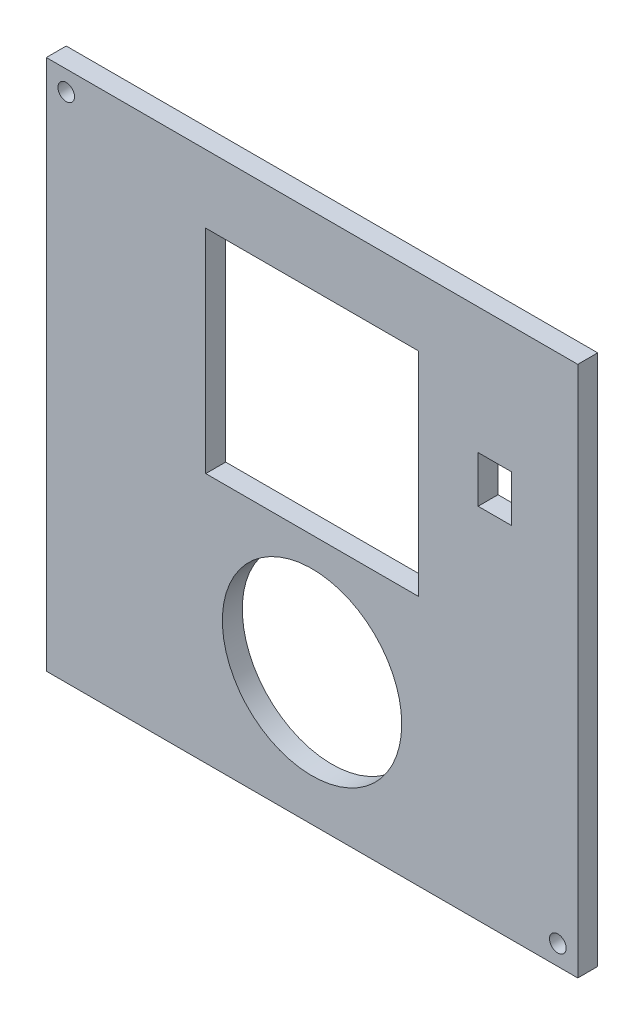
SolidWorks part; units mm, degrees
ref_plane "Front Plane" through (0, 0, 0) normal (0, 0, 1) x (1, 0, 0)
ref_plane "Top Plane" through (0, 0, 0) normal (0, 1, 0) x (1, 0, 0)
ref_plane "Right Plane" through (0, 0, 0) normal (1, 0, 0) x (0, 0, -1)
sketch "Sketch1" plane through (0, 0, 0) normal (0, 0, 1) x (1, 0, 0)
  line L1 (0, 0) -> (80, 0)
  line L2 (0, 0) -> (0, 80)
  line L3 (0, 80) -> (80, 80)
  line L4 (80, 0) -> (80, 80)
extrude "Boss-Extrude1" add sketch "Sketch1" along normal blind 3
sketch "Sketch2" plane through (0, 0, 3) normal (0, 0, 1) x (1, 0, 0)
  circle A0 centre (3, 77) radius 1.25
extrude "Cut-Extrude1" cut sketch "Sketch2" against normal blind 3 contours A0
sketch "Sketch3" plane through (0, 0, 3) normal (0, 0, 1) x (1, 0, 0)
  circle A0 centre (77, 3) radius 1.25
extrude "Cut-Extrude2" cut sketch "Sketch3" against normal blind 3
sketch "Sketch4" plane through (0, 3.7576, 3) normal (0, 0, 1) x (1, 0, 0)
  line L7 (40, 34) -> (56, 34)
  line L8 (56, 50) -> (56, 34)
  line L11 (40, 66) -> (56, 66)
  line L12 (56, 50) -> (56, 66)
  line L13 (24, 34) -> (40, 34)
  line L14 (24, 34) -> (24, 66)
  line L15 (24, 66) -> (40, 66)
  point P5 (0, 0)
  point P7 (0, 0)
  point P8 (0, 0)
extrude "Cut-Extrude3" cut sketch "Sketch4" against normal blind 3
sketch "Sketch5" plane through (0, 0.849, 3) normal (0, 0, 1) x (1, 0, 0)
  circle A0 centre (40, 19.0037) radius 13.5
  point P2 (0, 0)
extrude "Cut-Extrude4" cut sketch "Sketch5" against normal blind 3 contours A0
sketch "Sketch6" plane through (0, 0, 3) normal (0, 0, 1) x (1, 0, 0)
  line L5 (70, 59) -> (70, 54)
  line L6 (70, 54) -> (65, 54)
  line L7 (65, 59) -> (65, 54)
  line L9 (65, 59) -> (65, 61)
  line L10 (65, 61) -> (70, 61)
  line L11 (70, 59) -> (70, 61)
  point P0 (0, 0)
  point P8 (0, 0)
  point P12 (0, 0)
  point P13 (0, 0)
extrude "Cut-Extrude5" cut sketch "Sketch6" against normal blind 24
